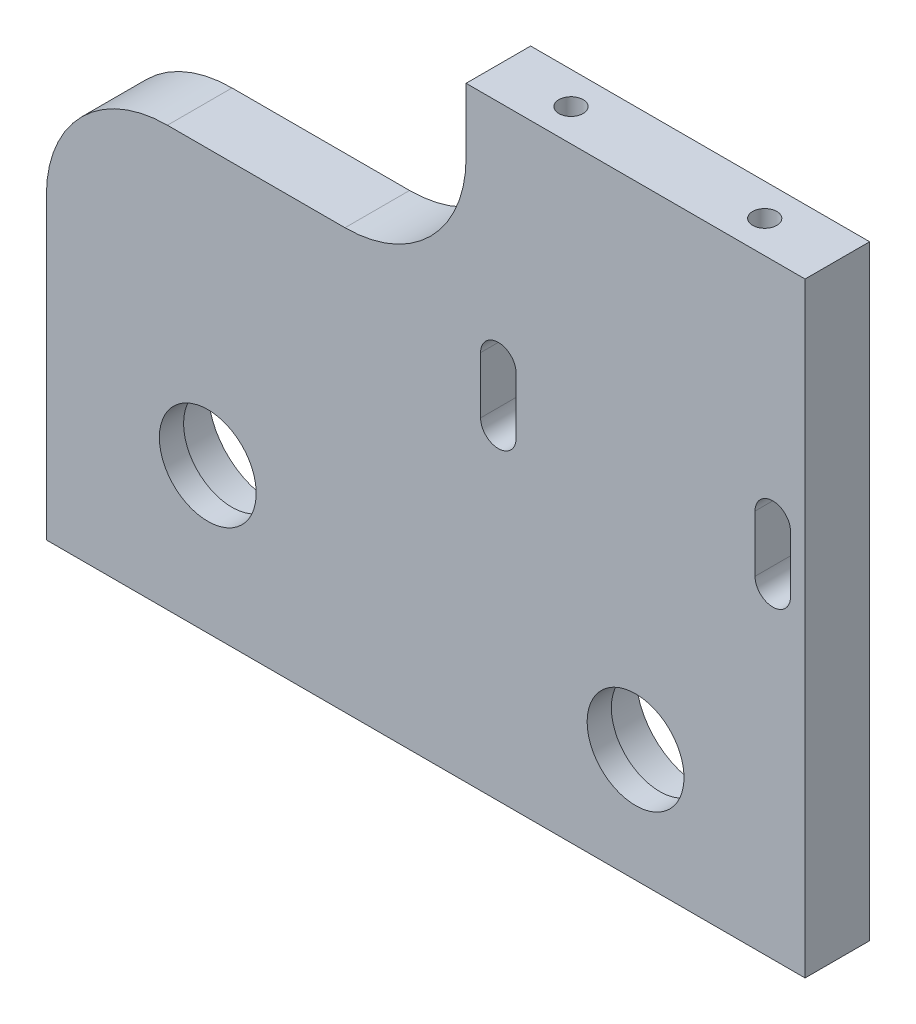
SolidWorks part; units mm, degrees
material "Alliage 1060"
ref_plane "Plan de face" through (0, 0, 0) normal (0, 0, 1) x (1, 0, 0)
ref_plane "Plan de dessus" through (0, 0, 0) normal (0, 1, 0) x (1, 0, 0)
ref_plane "Plan de droite" through (0, 0, 0) normal (1, 0, 0) x (0, 0, -1)
sketch "Esquisse1" plane through (0, 0, 0) normal (0, 0, 1) x (1, 0, 0)
  line L0 (52, 75) -> (52, 52)
  line L1 (0, 0) -> (94, 0)
  line L2 (0, 0) -> (0, 52)
  line L3 (52, 75) -> (94, 75)
  line L4 (94, 0) -> (94, 75)
  line L5 (52, 52) -> (0, 52)
  dimension "D1" = 94
  dimension "D2" = 75
  dimension "D3" = 52
  dimension "D4" = 42
extrude "Boss.-Extru.1" add sketch "Esquisse1" along normal blind 8
sketch "Esquisse2" plane through (0, 0, 0) normal (0, 0, -1) x (-1, 0, 0)
  line L0 (-20, 18) -> (-73, 14) construction
  line L1 (0, 0) -> (-94, 0) construction
  line L2 (0, 52) -> (0, 0) construction
  line L3 (-20, 18) -> (0, 18) construction
  line L4 (-20, 18) -> (-20, 0) construction
  line L5 (-73, 14) -> (-73, 0) construction
  circle A0 centre (-20, 18) radius 7.95
  circle A1 centre (-73, 14) radius 7.95
  dimension "D5" = 15.9
  dimension "D1" = 53
  dimension "D2" = 14
  dimension "D3" = 18
  dimension "D4" = 20
extrude "Enlèv. mat.-Extru.1" cut sketch "Esquisse2" against normal blind 5
sketch "Esquisse3" plane through (0, 0, 5) normal (0, 0, -1) x (-1, 0, 0)
  circle A0 centre (-73, 14) radius 6
  circle A1 centre (-20, 18) radius 6
  dimension "D1" = 12
extrude "Enlèv. mat.-Extru.2" cut sketch "Esquisse3" against normal through all
sketch "Esquisse4" plane through (0, 0, 0) normal (0, 0, -1) x (-1, 0, 0)
  line L0 (-90, 40) -> (-56, 40) construction
  line L1 (-94, 0) -> (-94, 75) construction
  line L2 (0, 0) -> (-94, 0) construction
  line L3 (-90, 40) -> (-90, 47) construction
  line L4 (-92.2, 40) -> (-92.2, 47)
  line L5 (-87.8, 40) -> (-87.8, 47)
  line L6 (-73, 40) -> (-73, 43.5) construction
  line L7 (-56, 40) -> (-56, 47) construction
  line L8 (-53.8, 40) -> (-53.8, 47)
  line L9 (-58.2, 40) -> (-58.2, 47)
  arc A2 (-92.2, 40) -> (-87.8, 40) centre (-90, 40) ccw
  arc A3 (-87.8, 47) -> (-92.2, 47) centre (-90, 47) ccw
  arc A4 (-53.8, 40) -> (-58.2, 40) centre (-56, 40) cw
  arc A5 (-58.2, 47) -> (-53.8, 47) centre (-56, 47) cw
  point P1 (-90, 43.5)
  point P15 (-56, 43.5)
  dimension "D1" = 4.4
  dimension "D2" = 34
  dimension "D3" = 4
  dimension "D4" = 40
  dimension "D5" = 7
extrude "Enlèv. mat.-Extru.3" cut sketch "Esquisse4" against normal through all
sketch "Esquisse5" plane through (0, 75, 0) normal (0, 1, 0) x (1, 0, 0)
  line L0 (94, -8) -> (94, 0) construction
  line L1 (61, -4) -> (85, -4) construction
  line L2 (94, 0) -> (52, 0) construction
  circle A0 centre (61, -4) radius 1.5
  circle A1 centre (85, -4) radius 1.5
  point P6 (94, -4)
  point P9 (73, 0)
  point P10 (73, -4)
  dimension "D1" = 3
  dimension "D2" = 9
extrude "Enlèv. mat.-Extru.4" cut sketch "Esquisse5" against normal blind 30
fillet "Congé1" radius 15 2 edges at (0, 52, 4) (52, 52, 4)
sketch "Esquisse6" plane through (0, 0, 0) normal (0, -1, 0) x (1, 0, 0)
  line L0 (6, 4) -> (88, 4) construction
  line L1 (0, 8) -> (94, 8) construction
  line L4 (94, 8) -> (94, 0) construction
  line L5 (0, 8) -> (0, 0) construction
  circle A0 centre (6, 4) radius 1.5
  circle A1 centre (88, 4) radius 1.5
  point P6 (47, 8)
  point P7 (47, 4)
  point P12 (0, 4)
  dimension "D1" = 3
  dimension "D2" = 6
extrude "Enlèv. mat.-Extru.5" cut sketch "Esquisse6" against normal blind 20
